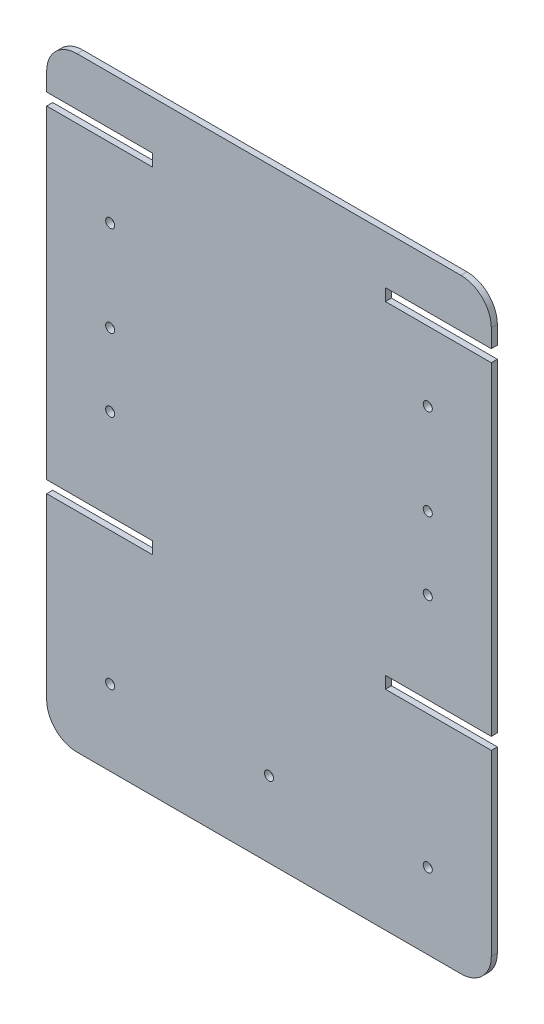
SolidWorks part; units mm, degrees
material "Plástico personalizado"
ref_plane "Plano frontal" through (0, 0, 0) normal (0, 0, 1) x (1, 0, 0)
ref_plane "Plano superior" through (0, 0, 0) normal (0, 1, 0) x (1, 0, 0)
ref_plane "Plano direito" through (0, 0, 0) normal (1, 0, 0) x (0, 0, -1)
sketch "Esboço1" plane through (0, 0, 0) normal (0, 0, 1) x (1, 0, 0)
  line L0 (-73.5, -27) -> (-73.5, 80)
  line L1 (-63.5, -100) -> (63.5, -100)
  line L2 (-73.5, -90) -> (-73.5, -31)
  line L3 (-63.5, 100) -> (63.5, 100)
  line L4 (73.5, -90) -> (73.5, -31)
  line L5 (-73.5, -100) -> (73.5, 100) construction
  line L6 (-73.5, 100) -> (73.5, -100) construction
  line L7 (-73.5, 80) -> (-38.5, 80)
  line L8 (0, 109.2953) -> (0, -108.6587) construction
  line L9 (-73.5, 84) -> (-38.5, 84)
  line L10 (-38.5, 80) -> (-38.5, 84)
  line L11 (-73.5, -27) -> (-38.5, -27)
  line L12 (-73.5, 84) -> (-73.5, 90)
  line L13 (-73.5, -31) -> (-38.5, -31)
  line L14 (-38.5, -27) -> (-38.5, -31)
  line L15 (38.5, -27) -> (38.5, -31)
  line L16 (73.5, -31) -> (38.5, -31)
  line L17 (73.5, -27) -> (38.5, -27)
  line L18 (38.5, 80) -> (38.5, 84)
  line L19 (73.5, 84) -> (38.5, 84)
  line L20 (73.5, 80) -> (38.5, 80)
  line L21 (73.5, -27) -> (73.5, 80)
  line L22 (73.5, 84) -> (73.5, 90)
  arc A0 (-63.5, -100) -> (-73.5, -90) centre (-63.5, -90) cw
  arc A1 (63.5, -100) -> (73.5, -90) centre (63.5, -90) ccw
  arc A2 (73.5, 90) -> (63.5, 100) centre (63.5, 90) ccw
  arc A3 (-63.5, 100) -> (-73.5, 90) centre (-63.5, 90) ccw
  point P0 (0, 0)
  dimension "D8" = 10
  dimension "D1" = 147
  dimension "D2" = 200
  dimension "D3" = 35
  dimension "D4" = 20
  dimension "D5" = 4
  dimension "D6" = 107
  dimension "D7" = 4
extrude "Ressalto-extrusão1" add sketch "Esboço1" along normal blind 2
sketch "Esboço2" plane through (0, 0, 2) normal (0, 0, 1) x (1, 0, 0)
  line L0 (-38.5, 80) -> (-73.5, 80) construction
  line L1 (-63.5, -100) -> (63.5, -100) construction
  line L2 (-73.5, -31) -> (-73.5, -90) construction
  line L3 (-73.5, 80) -> (-73.5, -27) construction
  line L4 (0, 112.3955) -> (0, -112.4668) construction
  circle A0 centre (-52.5, 57) radius 1.5
  circle A1 centre (-52.5, 27) radius 1.5
  circle A2 centre (-52.5, 3) radius 1.5
  circle A3 centre (-52.5, -75) radius 1.5
  circle A4 centre (52.5, 57) radius 1.5
  circle A5 centre (52.5, -75) radius 1.5
  circle A6 centre (52.5, 3) radius 1.5
  circle A7 centre (52.5, 27) radius 1.5
  circle A8 centre (0, -75) radius 1.5
  dimension "D5" = 3
  dimension "D1" = 23
  dimension "D2" = 53
  dimension "D3" = 77
  dimension "D4" = 25
  dimension "D6" = 21
  dimension "D7" = 21
extrude "Corte-extrusão1" cut sketch "Esboço2" against normal blind 2
sketch "Esboço3" plane through (0, 0, 0) normal (0, 1, 0) x (1, 0, 0)
  line L0 (-63.5, -2) -> (63.5, -2) construction
  point P0 (0, -15.5)
  dimension "D1" = 13.5
